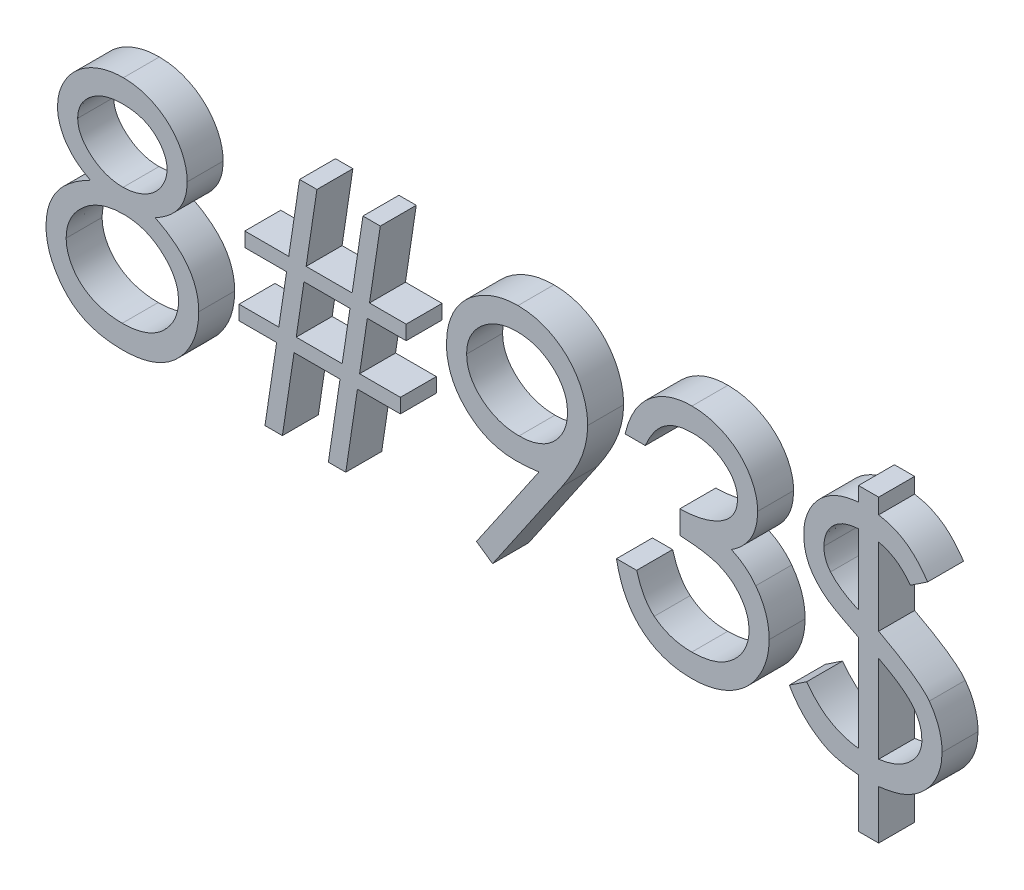
SolidWorks part; units mm, degrees
ref_plane "Front Plane" through (0, 0, 0) normal (0, 0, 1) x (1, 0, 0)
ref_plane "Top Plane" through (0, 0, 0) normal (0, 1, 0) x (1, 0, 0)
ref_plane "Right Plane" through (0, 0, 0) normal (1, 0, 0) x (0, 0, -1)
sketch "Sketch1" plane through (0, 0, 0) normal (0, 0, 1) x (1, 0, 0)
  line L0 (-35.56, 0) -> (35.56, 0) construction
  text T0 "8#93$\r\n" font "Century Gothic" height in points 60
  point P4 (0, 0)
  dimension "D1" = 71.12
extrude "Boss-Extrude1" add sketch "Sketch1" along normal blind 2.54
